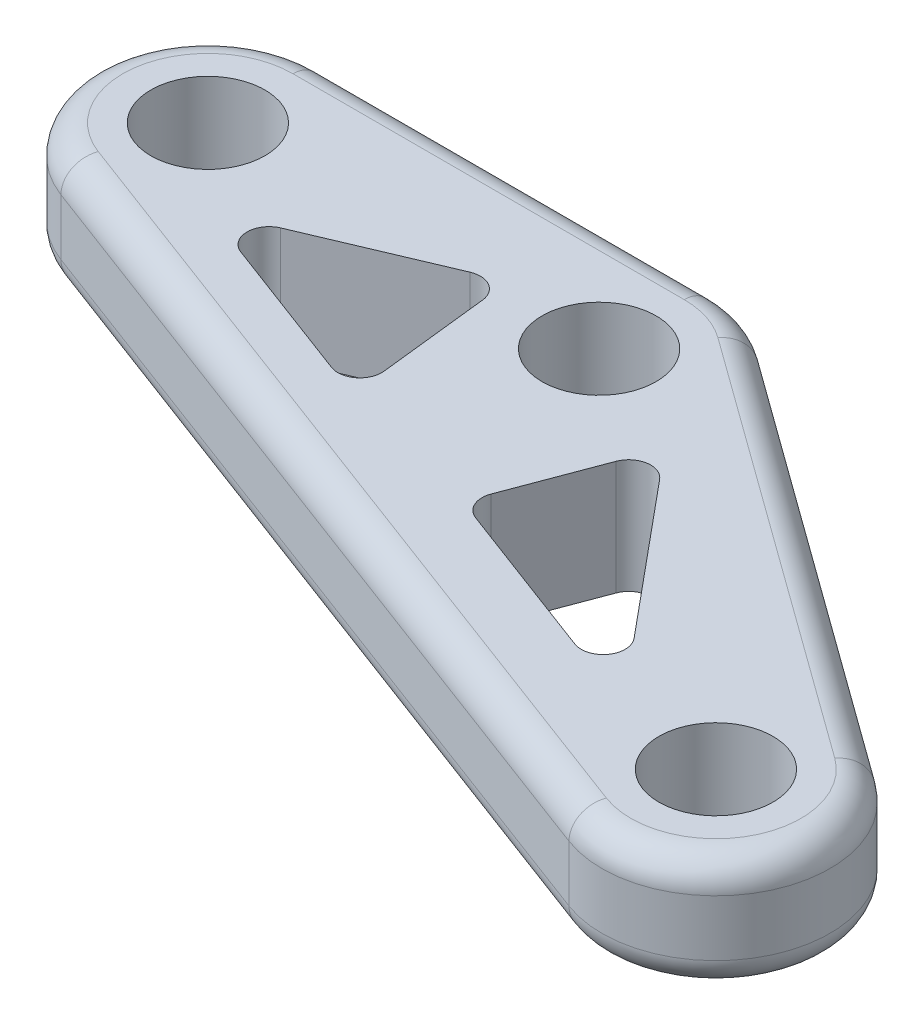
SolidWorks part; units mm, degrees
ref_plane "Front Plane" through (0, 0, 0) normal (0, 0, 1) x (1, 0, 0)
ref_plane "Top Plane" through (0, 0, 0) normal (0, 1, 0) x (1, 0, 0)
ref_plane "Right Plane" through (0, 0, 0) normal (1, 0, 0) x (0, 0, -1)
sketch "Sketch1" plane through (0, 0, 0) normal (0, 1, 0) x (1, 0, 0)
  line L0 (-37.807, -9.3611) -> (33.5246, -36.161)
  line L1 (42.9034, -18.698) -> (5.8617, 8.1019)
  line L2 (-34.29, 10) -> (0, 10)
  line L3 (37.0417, -26.7999) -> (0, 0) construction
  line L4 (0, 0) -> (-34.29, 0) construction
  line L5 (-34.29, 0) -> (37.0417, -26.7999) construction
  line L6 (-7.3733, -14.2442) -> (-27.5578, -6.6608)
  line L7 (-27.5578, -6.6608) -> (-9.0892, 1.1651)
  line L8 (-9.0892, 1.1651) -> (-7.3733, -14.2442)
  line L9 (10.448, -4.7064) -> (5.617, -17.5647)
  line L10 (5.617, -17.5647) -> (28.1474, -26.0296)
  line L11 (28.1474, -26.0296) -> (10.448, -4.7064)
  arc A0 (-37.807, -9.3611) -> (-34.29, 10) centre (-34.29, 0) cw
  arc A1 (5.8617, 8.1019) -> (0, 10) centre (0, 0) ccw
  arc A2 (33.5246, -36.161) -> (42.9034, -18.698) centre (37.0417, -26.7999) ccw
  circle A3 centre (-34.29, 0) radius 5
  circle A4 centre (0, 0) radius 5
  circle A5 centre (37.0417, -26.7999) radius 5
  dimension "D4" = 10
  dimension "D5" = 10
  dimension "D1" = 76.2
  dimension "D2" = 34.29
  dimension "D3" = 45.72
extrude "Boss-Extrude1" add sketch "Sketch1" along normal blind 10
fillet "Fillet1" radius 2.54 12 edges at (-44.129, 0, -1.7873) (-17.145, 0, -10) (3.0807, 0, -9.5136) (24.3826, 0, 5.2981) (45.8515, 0, 31.5313) (-44.129, 10, -1.7873) (-17.145, 10, -10) (3.0807, 10, -9.5136) (24.3826, 10, 5.2981) (45.8515, 10, 31.5313) (-2.1412, 0, 22.761) (-2.1412, 10, 22.761)
scale "Scale1" scale about centroid uniform scaling yes scale factor 0.66
fillet "Fillet2" radius 1.27 6 edges at (4.4985, 5, 15.1172) (7.687, 5, 6.6307) (19.3686, 5, 20.704) (-4.0751, 5, 12.9257) (-17.3969, 5, 7.9206) (-5.2076, 5, 2.7556)
